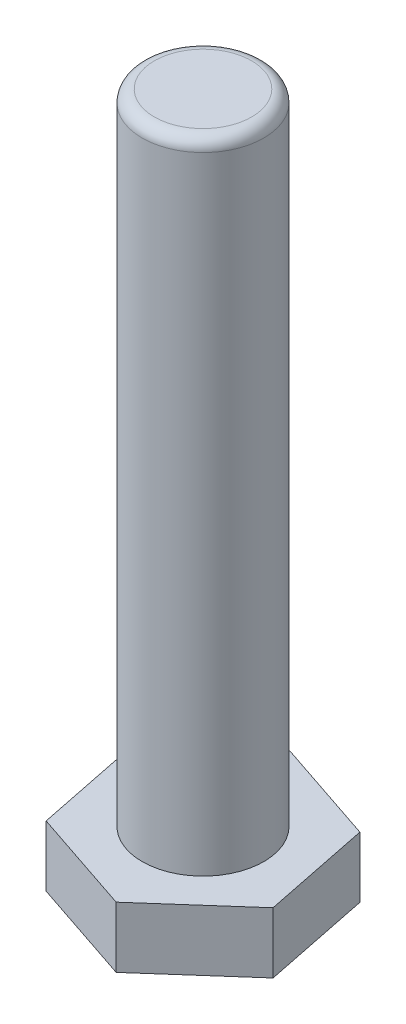
SolidWorks part; units mm, degrees
ref_plane "Plan de face" through (0, 0, 0) normal (0, 0, 1) x (1, 0, 0)
ref_plane "Plan de dessus" through (0, 0, 0) normal (0, 1, 0) x (1, 0, 0)
ref_plane "Plan de droite" through (0, 0, 0) normal (1, 0, 0) x (0, 0, -1)
sketch "Esquisse1" plane through (0, 0, 0) normal (0, 1, 0) x (1, 0, 0)
  line L1 (-13.6895, -12.0963) -> (3.631, -17.9037)
  line L2 (3.631, -17.9037) -> (17.3205, -5.8073)
  line L3 (17.3205, -5.8073) -> (13.6895, 12.0963)
  line L4 (13.6895, 12.0963) -> (-3.631, 17.9037)
  line L5 (-3.631, 17.9037) -> (-17.3205, 5.8073)
  line L6 (-17.3205, 5.8073) -> (-13.6895, -12.0963)
  circle A0 centre (0, 0) radius 15.8207 construction
  dimension "D1" = 30
extrude "Boss.-Extru.1" add sketch "Esquisse1" along normal blind 10
sketch "Esquisse2" plane through (0, 10, 0) normal (0, 1, 0) x (1, 0, 0)
  circle A0 centre (0, 0) radius 10
extrude "Boss.-Extru.2" add sketch "Esquisse2" along normal blind 105
fillet "Congé1" radius 2 1 edges at (0, 115, 10)
